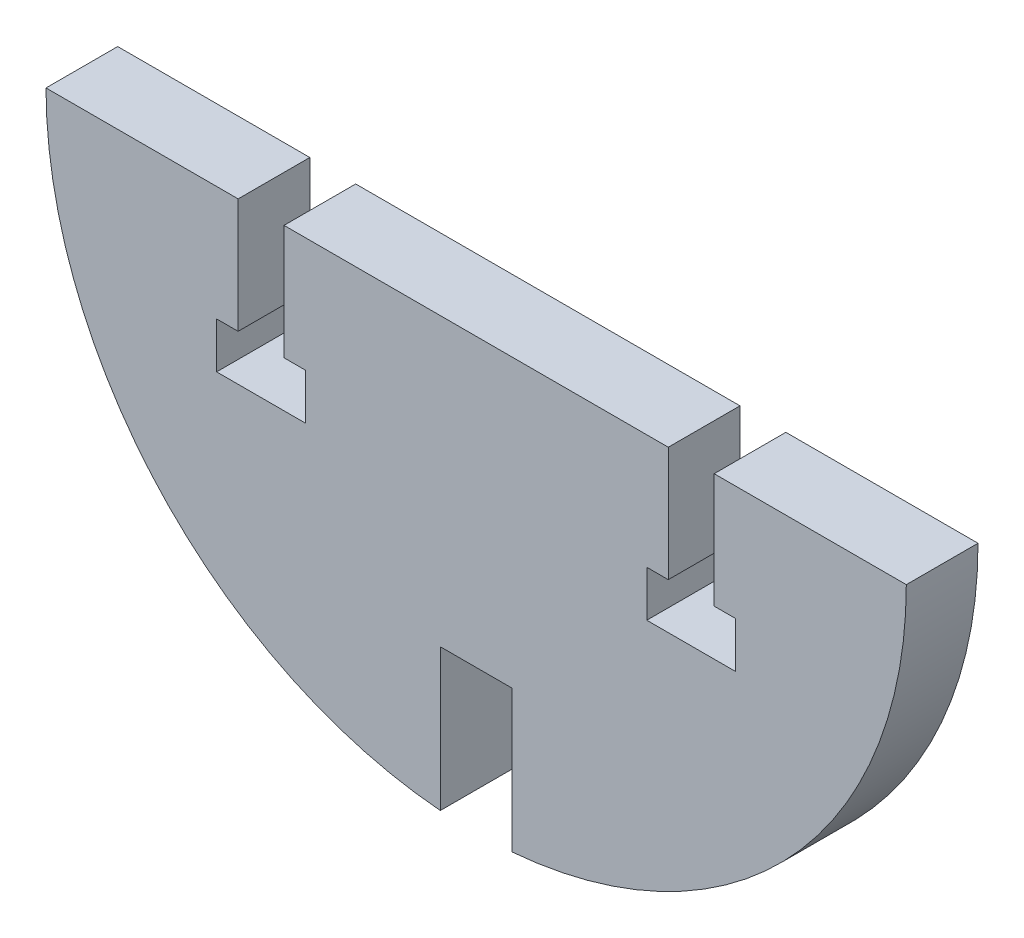
SolidWorks part; units mm, degrees
ref_plane "Front Plane" through (0, 0, 0) normal (0, 0, 1) x (1, 0, 0)
ref_plane "Top Plane" through (0, 0, 0) normal (0, 1, 0) x (1, 0, 0)
ref_plane "Right Plane" through (0, 0, 0) normal (1, 0, 0) x (0, 0, -1)
sketch "Sketch1" plane through (0, 0, 0) normal (0, 0, 1) x (1, 0, 0)
  line L0 (3.175, 584.2) -> (3.175, 541.6718) construction
  line L1 (6.35, 584.2) -> (0, 584.2) construction
  line L2 (3.175, 584.2) -> (20.193, 584.2)
  line L3 (3.175, 584.2) -> (-13.843, 584.2)
  line L4 (0, 546.2325) -> (0, 558.8)
  line L5 (0, 584.2) -> (0, 406.4) construction
  line L6 (0, 558.8) -> (6.35, 558.8)
  line L7 (6.35, 558.8) -> (6.35, 546.2325)
  line L8 (6.35, 406.4) -> (6.35, 584.2) construction
  line L9 (-15.875, 584.2) -> (-15.875, 558.8) construction
  line L10 (-17.907, 584.2) -> (-17.907, 574.04)
  line L11 (-17.907, 574.04) -> (-19.812, 574.04)
  line L12 (-19.812, 574.04) -> (-19.812, 572.554)
  line L13 (-19.812, 572.554) -> (-19.812, 569.976)
  line L14 (-19.812, 569.976) -> (-11.938, 569.976)
  line L15 (-11.938, 572.554) -> (-11.938, 569.976)
  line L16 (-11.938, 574.04) -> (-11.938, 572.554)
  line L17 (-13.843, 584.2) -> (-13.843, 574.04)
  line L18 (-17.907, 584.2) -> (-34.925, 584.2)
  line L19 (-13.843, 574.04) -> (-11.938, 574.04)
  line L20 (22.225, 584.2) -> (22.225, 558.8) construction
  line L21 (20.193, 574.04) -> (18.288, 574.04)
  line L22 (20.193, 584.2) -> (20.193, 574.04)
  line L23 (18.288, 574.04) -> (18.288, 572.554)
  line L24 (18.288, 572.554) -> (18.288, 569.976)
  line L25 (26.162, 569.976) -> (18.288, 569.976)
  line L26 (26.162, 572.554) -> (26.162, 569.976)
  line L27 (26.162, 574.04) -> (26.162, 572.554)
  line L28 (24.257, 574.04) -> (26.162, 574.04)
  line L29 (24.257, 584.2) -> (24.257, 574.04)
  line L30 (24.257, 584.2) -> (41.275, 584.2)
  arc A0 (-34.925, 584.2) -> (0, 546.2325) centre (3.175, 584.2) ccw
  arc A1 (6.35, 546.2325) -> (41.275, 584.2) centre (3.175, 584.2) ccw
  point P26 (-15.875, 569.976)
  point P42 (22.225, 569.976)
  dimension "D3" = 38.1
  dimension "D1" = 38.1
  dimension "D2" = 38.1
  dimension "D4" = 14.224
  dimension "D5" = 4.064
  dimension "D6" = 2.032
  dimension "D7" = 3.937
extrude "Boss-Extrude1" add sketch "Sketch1" along normal blind 6.35
